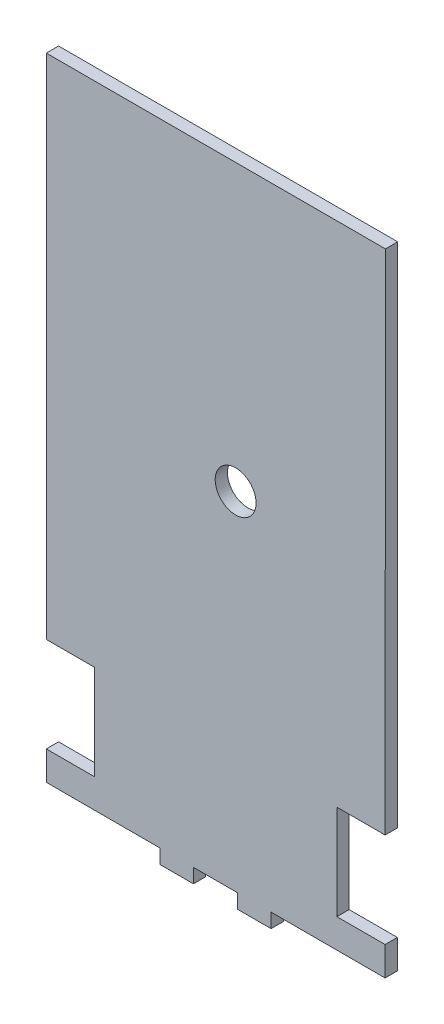
SolidWorks part; units mm, degrees
ref_plane "Alzado" through (0, 0, 0) normal (0, 0, 1) x (1, 0, 0)
ref_plane "Planta" through (0, 0, 0) normal (0, 1, 0) x (1, 0, 0)
ref_plane "Vista lateral" through (0, 0, 0) normal (1, 0, 0) x (0, 0, -1)
sketch "Model" plane through (0, 0, 0) normal (0, 0, 1) x (1, 0, 0)
  line L0 (-6.2522, 97.6924) -> (-6.2522, -12.9923)
  line L1 (-6.2522, -12.9923) -> (-6.2522, -26.5699)
  line L2 (-6.2522, -26.5699) -> (5.5478, -26.5699)
  line L3 (5.5478, -26.5699) -> (5.5478, -49.7699)
  line L4 (5.5478, -49.7699) -> (-6.2522, -49.7699)
  line L5 (-6.2522, -49.7699) -> (-6.2522, -56.8546)
  line L6 (-6.2522, -56.8546) -> (21.5552, -56.8687)
  line L7 (21.5552, -56.8687) -> (21.5552, -60.3622)
  line L8 (21.5552, -60.3622) -> (29.7552, -60.3622)
  line L9 (29.7552, -60.3622) -> (29.7552, -56.8622)
  line L10 (29.7552, -56.8622) -> (40.5552, -56.8622)
  line L11 (40.5552, -56.8622) -> (40.5552, -60.3622)
  line L12 (40.5552, -60.3622) -> (48.7552, -60.3622)
  line L13 (48.7552, -60.3622) -> (48.7552, -56.8622)
  line L14 (48.7552, -56.8622) -> (76.6552, -56.8699)
  line L15 (76.6552, -56.8699) -> (76.6552, -49.7699)
  line L16 (76.6552, -49.7699) -> (64.8552, -49.7699)
  line L17 (64.8552, -49.7699) -> (64.8552, -26.5699)
  line L18 (64.8552, -26.5699) -> (76.6552, -26.5699)
  line L19 (76.6552, -26.5699) -> (76.7478, 97.6924)
  line L20 (76.7478, 97.6924) -> (-6.2522, 97.6924)
  circle A0 centre (40.0856, 27.9706) radius 5
extrude "Saliente-Extruir1" add sketch "Model" along normal blind 3
